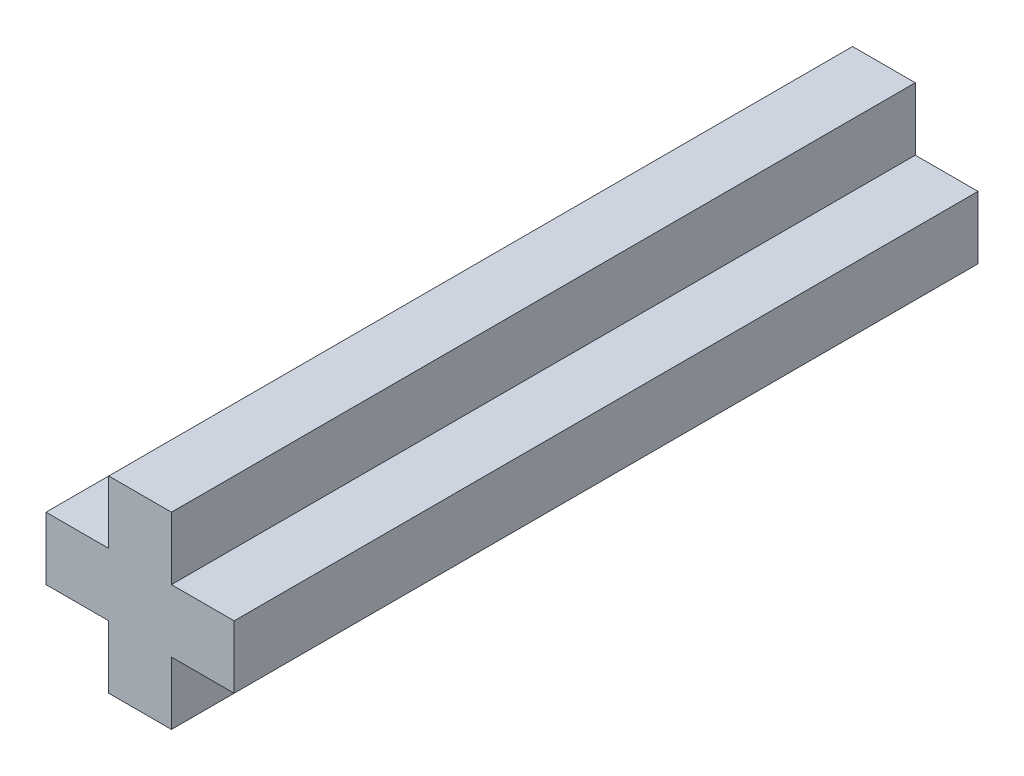
SolidWorks part; units mm, degrees
ref_plane "Front Plane" through (0, 0, 0) normal (0, 0, 1) x (1, 0, 0)
ref_plane "Top Plane" through (0, 0, 0) normal (0, 1, 0) x (1, 0, 0)
ref_plane "Right Plane" through (0, 0, 0) normal (1, 0, 0) x (0, 0, -1)
sketch "Sketch1" plane through (0, 0, 0) normal (0, 0, 1) x (1, 0, 0)
  line L0 (-4, 0) -> (4, 0) construction
  line L1 (0, 4) -> (0, -4) construction
  line L2 (-3.7947, 1.2649) -> (-3.7947, -1.2649)
  line L3 (-3.7947, 1.2649) -> (-1.2649, 1.2649)
  line L4 (-1.2649, 1.2649) -> (-1.2649, 3.7947)
  line L5 (-1.2649, 3.7947) -> (1.2649, 3.7947)
  line L6 (1.2649, 3.7947) -> (1.2649, 1.2649)
  line L7 (1.2649, 1.2649) -> (3.7947, 1.2649)
  line L8 (3.7947, 1.2649) -> (3.7947, -1.2649)
  line L9 (3.7947, -1.2649) -> (1.2649, -1.2649)
  line L10 (1.2649, -1.2649) -> (1.2649, -3.7947)
  line L11 (1.2649, -3.7947) -> (-1.2649, -3.7947)
  line L12 (-1.2649, -3.7947) -> (-1.2649, -1.2649)
  line L13 (-1.2649, -1.2649) -> (-3.7947, -1.2649)
  circle A0 centre (0, 0) radius 4 construction
  point P6 (0, 0)
  point P8 (0, 0)
  point P9 (-1.2649, -2.5298)
  point P12 (-3.7947, 0)
  point P23 (0, 3.7947)
  point P24 (-1.0872, 1.0872)
  point P25 (3.7936, 1.2682)
  dimension "D1" = 8
extrude "Boss-Extrude1" add sketch "Sketch1" along normal blind 30
